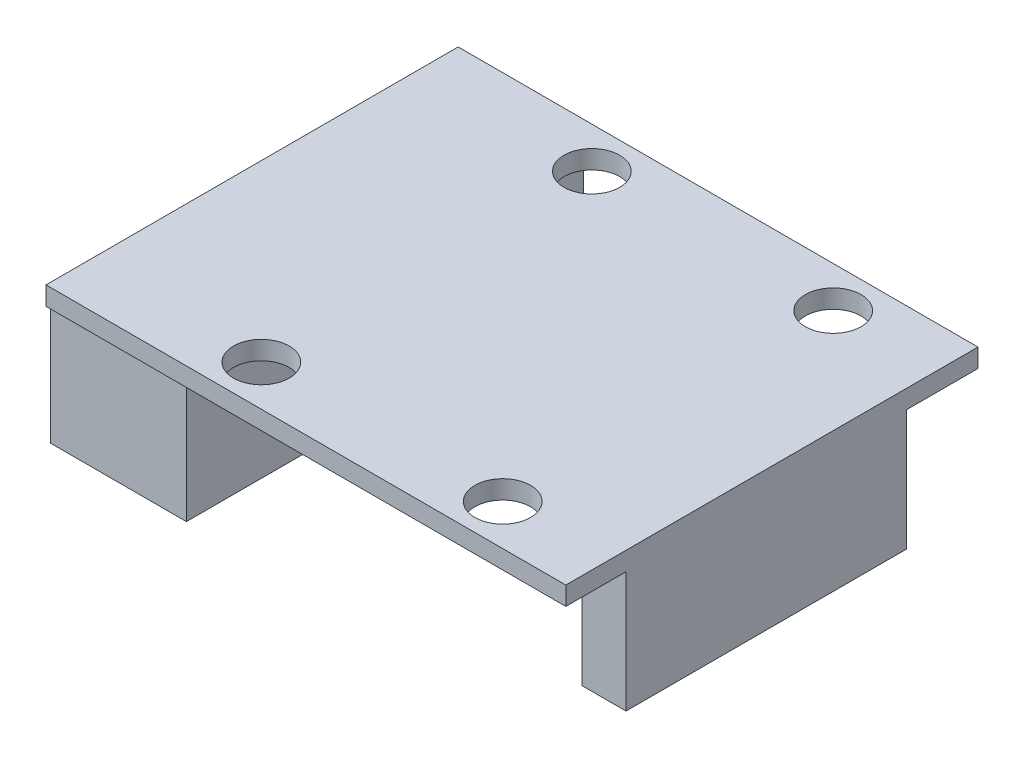
SolidWorks part; units mm, degrees
ref_plane "Front Plane" through (0, 0, 0) normal (0, 0, 1) x (1, 0, 0)
ref_plane "Top Plane" through (0, 0, 0) normal (0, 1, 0) x (1, 0, 0)
ref_plane "Right Plane" through (0, 0, 0) normal (1, 0, 0) x (0, 0, -1)
sketch "Sketch1" plane through (0, 0, 0) normal (0, 1, 0) x (1, 0, 0)
  line L0 (-187.8326, 332.946) -> (464.1674, 332.946) construction
  line L1 (0, 0) -> (28, 0)
  line L2 (0, 0) -> (0, 22.2)
  line L3 (0, 22.2) -> (28, 22.2)
  line L4 (28, 0) -> (28, 22.2)
  line L5 (0.0016, 0.0759) -> (28.0016, 0.0759) construction
  circle A0 centre (9.4, 20) radius 1.5
  circle A1 centre (22.4, 20) radius 1.5
  circle A2 centre (22.4, 2.2) radius 1.5
  circle A3 centre (9.4, 2.2) radius 1.5
  dimension "D4" = 3
  dimension "D1" = 28
  dimension "D2" = 22.2
  dimension "D3" = 28
  dimension "D5" = 2.2
  dimension "D6" = 2.2
  dimension "D7" = 5.6
  dimension "D8" = 13
extrude "Boss-Extrude1" add sketch "Sketch1" along normal blind 1
sketch "Sketch2" plane through (0, 0, 0) normal (0, -1, 0) x (1, 0, 0)
  line L0 (0, -22.2) -> (0, 0) construction
  line L1 (0, -21.8039) -> (7.1406, -21.8039)
  line L2 (0, -21.8039) -> (0, -11.4291)
  line L3 (0, -11.4291) -> (7.1406, -11.4291)
  line L4 (7.1406, -21.8039) -> (7.1406, -11.4291)
  line L5 (28, 0) -> (28, -22.2) construction
  line L6 (0, -10.5602) -> (7.3249, -10.5602)
  line L7 (0, -10.5602) -> (0, -0.2381)
  line L8 (0, -0.2381) -> (7.3249, -0.2381)
  line L9 (7.3249, -10.5602) -> (7.3249, -0.2381)
  line L10 (25.6255, -18.3544) -> (28, -18.3544)
  line L11 (25.6255, -18.3544) -> (25.6255, -3.24)
  line L12 (25.6255, -3.24) -> (28, -3.24)
  line L13 (28, -18.3544) -> (28, -3.24)
extrude "Boss-Extrude2" add sketch "Sketch2" along normal blind 6.5
